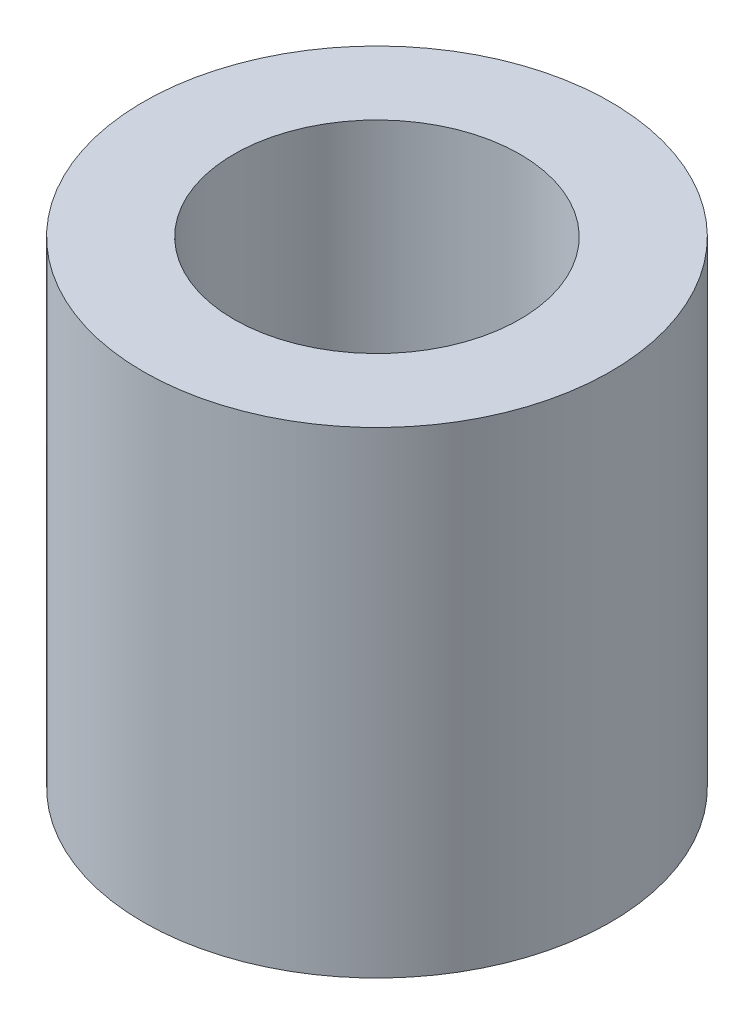
SolidWorks part; units mm, degrees
ref_plane "Ön Düzlem" through (0, 0, 0) normal (0, 0, 1) x (1, 0, 0)
ref_plane "Üst Düzlem" through (0, 0, 0) normal (0, 1, 0) x (1, 0, 0)
ref_plane "Sağ Düzlem" through (0, 0, 0) normal (1, 0, 0) x (0, 0, -1)
sketch "Sketch1" plane through (0, 0, 0) normal (0, 1, 0) x (1, 0, 0)
  circle A0 centre (0, 0) radius 4.9
  dimension "D1" = 9.8
extrude "Boss-Extrude1" add sketch "Sketch1" along normal blind 10
ref_plane "Plane1" through (0, 5, 0) normal (0, 1, 0) x (1, 0, 0)
sketch "Sketch5" plane through (0, 5, 0) normal (0, 1, 0) x (1, 0, 0)
  line L0 (-4, -2.3094) -> (-4, -2.8302)
  line L1 (4, -2.3094) -> (4, 2.3094)
  line L2 (4, 2.3094) -> (0, 4.6188)
  line L3 (0, 4.6188) -> (-4, 2.3094)
  line L4 (-4, 2.3094) -> (-4, -2.3094)
  line L5 (-4, -2.3094) -> (0, -4.6188)
  line L6 (0, -4.6188) -> (4, -2.3094)
  line L7 (4, -2.3094) -> (4, -2.8302)
  circle A0 centre (0, 0) radius 4 construction
  circle A1 centre (0, 0) radius 4.9 construction
  circle A3 centre (0, 0) radius 4.9
  arc A4 (-4, -2.8302) -> (4, -2.8302) centre (0, 0) ccw
  point P1 (4, 0)
  dimension "D1" = 8
  dimension "D2" = 0
sketch "Sketch6" plane through (0, 10, 0) normal (0, 1, 0) x (1, 0, 0)
  circle A0 centre (0, 0) radius 3
  dimension "D1" = 6
extrude "Cut-Extrude3" cut sketch "Sketch6" against normal through all
equation "\"D19@Cut-Extrude1\"=\"SW-CenterofMassY\"/2"
